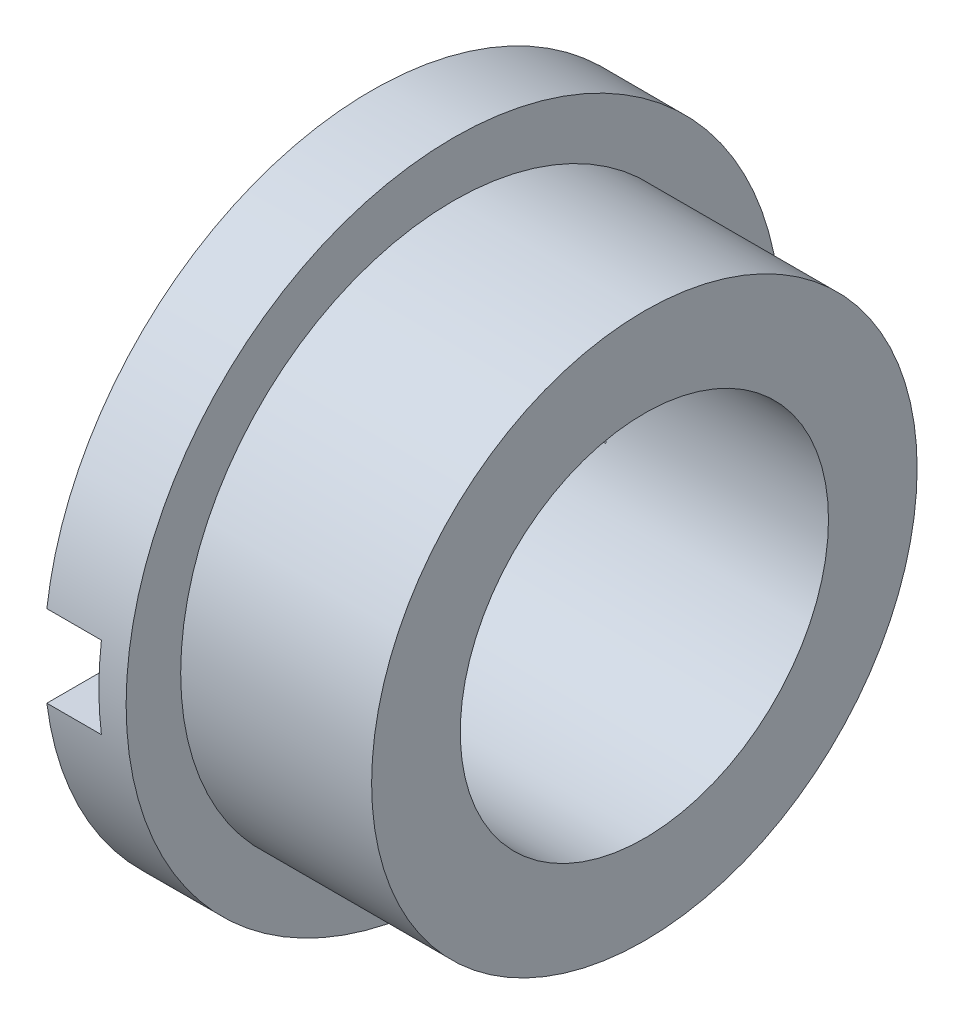
SolidWorks part; units mm, degrees
ref_plane "Plan de face" through (0, 0, 0) normal (0, 0, 1) x (1, 0, 0)
ref_plane "Plan de dessus" through (0, 0, 0) normal (0, 1, 0) x (1, 0, 0)
ref_plane "Plan de droite" through (0, 0, 0) normal (1, 0, 0) x (0, 0, -1)
sketch "Esquisse1" plane through (0, 0, 0) normal (1, 0, 0) x (0, 0, -1)
  circle A0 centre (0, 0) radius 5
  circle A1 centre (0, 0) radius 3.375
  dimension "D1" = 10
  dimension "D2" = 6.75
extrude "Extrusion1" add sketch "Esquisse1" along normal blind 3.5 and the other way blind 1.5
sketch "Esquisse2" plane through (0, 0, 0) normal (1, 0, 0) x (0, 0, -1)
  circle A0 centre (0, 0) radius 3.375
  circle A1 centre (0, 0) radius 6
  circle A2 centre (0, 0) radius 3.375 construction
  dimension "D1" = 12
extrude "Extrusion2" add sketch "Esquisse2" against normal up to surface (1.5 mm away) up to face at (-1.5, 0, -3.375)
sketch "Esquisse3" plane through (0, 0, 0) normal (0, 0, 1) x (1, 0, 0)
  line L0 (-1.5, 6) -> (-1.5, -6) construction
  line L1 (-1.5, 0.75) -> (-0.5, 0.75)
  line L2 (-1.5, 0.75) -> (-1.5, -0.75)
  line L3 (-1.5, -0.75) -> (-0.5, -0.75)
  line L4 (-0.5, 0.75) -> (-0.5, -0.75)
  line L5 (0, 0) -> (-3.9679, 0) construction
  dimension "D1" = 1.5
  dimension "D2" = 1
extrude "Enlèv. mat.-Extru.1" cut sketch "Esquisse3" against normal through all and the other way through all
